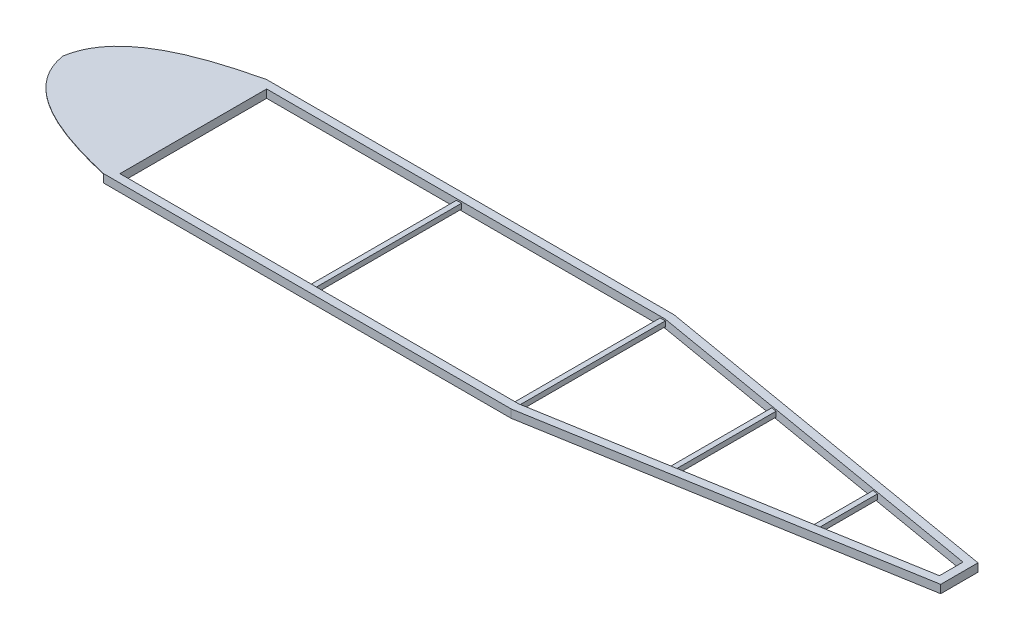
SolidWorks part; units mm, degrees
material "6061-T6 (SS)"
ref_plane "Front" through (0, 0, 0) normal (0, 0, 1) x (1, 0, 0)
ref_plane "Top" through (0, 0, 0) normal (0, 1, 0) x (1, 0, 0)
ref_plane "Right" through (0, 0, 0) normal (1, 0, 0) x (0, 0, -1)
sketch "Sketch1" plane through (0, 0, 0) normal (0, 1, 0) x (1, 0, 0)
  line L0 (0, 508) -> (0, -508)
  line L1 (0, -508) -> (2540, -508)
  line L2 (2540, -508) -> (4826, -116.205)
  line L3 (4826, -116.205) -> (4826, 116.205)
  line L4 (4826, 116.205) -> (2540, 508)
  line L5 (2540, 508) -> (0, 508)
  line L6 (2535.6782, 457.2) -> (50.8, 457.2)
  line L7 (50.8, 457.2) -> (50.8, -457.2)
  line L8 (50.8, -457.2) -> (2535.6782, -457.2)
  line L9 (2535.6782, -457.2) -> (4775.2, -73.3709)
  line L10 (4775.2, -73.3709) -> (4775.2, 73.3709)
  line L11 (4775.2, 73.3709) -> (2535.6782, 457.2)
  point P3 (0, 0)
  point P8 (4826, 0)
  dimension "D1" = 1016
  dimension "D2" = 2540
  dimension "D3" = 4826
  dimension "D4" = 232.41
  dimension "D5" = 50.8
extrude "Boss-Extrude1" add sketch "Sketch1" along normal blind 50.8
ref_plane "Plane1" through (0, 3.175, 0) normal (0, 1, 0) x (1, 0, 0)
sketch "Sketch2" plane through (0, 3.175, 0) normal (0, 1, 0) x (1, 0, 0)
  line L6 (2535.9483, 460.375) -> (47.625, 460.375)
  line L7 (47.625, 460.375) -> (47.625, -460.375)
  line L8 (47.625, -460.375) -> (2535.9483, -460.375)
  line L9 (2535.9483, -460.375) -> (4778.375, -76.048)
  line L10 (4778.375, -76.048) -> (4778.375, 76.048)
  line L11 (4778.375, 76.048) -> (2535.9483, 460.375)
  line L12 (3.175, -504.825) -> (2539.7299, -504.825)
  line L13 (2539.7299, -504.825) -> (4822.825, -113.5279)
  line L14 (4822.825, -113.5279) -> (4822.825, 113.5279)
  line L15 (4822.825, 113.5279) -> (2539.7299, 504.825)
  line L16 (2539.7299, 504.825) -> (3.175, 504.825)
  line L17 (3.175, 504.825) -> (3.175, -504.825)
  line L18 (3.175, -504.825) -> (2539.7299, -504.825)
  line L19 (2539.7299, -504.825) -> (4822.825, -113.5279)
  line L20 (4822.825, -113.5279) -> (4822.825, 113.5279)
  line L21 (4822.825, 113.5279) -> (2539.7299, 504.825)
  line L22 (2539.7299, 504.825) -> (3.175, 504.825)
  line L23 (3.175, 504.825) -> (3.175, -504.825)
  dimension "D1" = 3.175
  dimension "D2" = 44.45
extrude "Cut-Extrude1" cut sketch "Sketch2" along normal blind 44.45
sketch "Sketch3" plane through (0, 0, -457.2) normal (0, 0, 1) x (1, 0, 0)
  line L0 (2535.6782, 41.275) -> (2535.6782, 9.525)
  line L1 (2535.6782, 50.8) -> (50.8, 50.8) construction
  line L2 (1262.5032, 38.1) -> (1237.1032, 38.1)
  line L3 (2535.6782, 50.8) -> (2535.6782, 0) construction
  line L4 (2535.6782, 41.275) -> (2503.9282, 41.275)
  line L5 (2503.9282, 41.275) -> (2503.9282, 9.525)
  line L6 (2503.9282, 9.525) -> (2535.6782, 9.525)
  line L7 (2532.5032, 38.1) -> (2507.1032, 38.1)
  line L8 (2507.1032, 38.1) -> (2507.1032, 12.7)
  line L9 (2507.1032, 12.7) -> (2532.5032, 12.7)
  line L10 (2532.5032, 38.1) -> (2532.5032, 12.7)
  line L11 (1265.6782, 41.275) -> (1233.9282, 41.275)
  line L12 (1233.9282, 41.275) -> (1233.9282, 9.525)
  line L13 (1233.9282, 9.525) -> (1265.6782, 9.525)
  line L14 (1237.1032, 12.7) -> (1262.5032, 12.7)
  line L15 (1265.6782, 41.275) -> (1265.6782, 9.525)
  line L16 (1262.5032, 38.1) -> (1262.5032, 12.7)
  line L17 (1237.1032, 38.1) -> (1237.1032, 12.7)
  point P5 (2535.6782, 25.4)
  point P8 (2535.6782, 25.4)
  dimension "D1" = 9.525
  dimension "D2" = 3.175
  dimension "D3" = 2
extrude "Boss-Extrude2" add sketch "Sketch3" along normal up to next
sketch "Sketch4" plane through (50.8, 0, 0) normal (1, 0, 0) x (0, 0, -1)
  line L0 (0, 50.8) -> (0, 0) construction
  line L1 (457.2, 50.8) -> (-457.2, 50.8) construction
  point P7 (0, 25.4)
sketch "Sketch5" plane through (4775.2, 0, 0) normal (-1, 0, 0) x (0, 0, 1)
  line L0 (0, 50.8) -> (0, 0) construction
  line L1 (73.3709, 50.8) -> (-73.3709, 50.8) construction
  line L2 (73.3709, 0) -> (-73.3709, 0) construction
  point P6 (0, 25.4)
ref_plane "Plane2" through (0, 0, 0) normal (0, 0, 1) x (1, 0, 0)
sketch "Sketch8" plane through (0, 0, 0) normal (0, 0, 1) x (1, 0, 0)
  line L0 (50.8, 25.4) -> (4775.2, 25.4) construction
  line L1 (50.8, 50.8) -> (50.8, 0) construction
  line L2 (3340.1, 38.1) -> (3365.5, 38.1)
  line L3 (3336.925, 41.275) -> (3368.675, 41.275)
  line L4 (3336.925, 41.275) -> (3336.925, 9.525)
  line L5 (3336.925, 9.525) -> (3368.675, 9.525)
  line L6 (3368.675, 41.275) -> (3368.675, 9.525)
  line L7 (3336.925, 41.275) -> (3368.675, 9.525) construction
  line L8 (3336.925, 9.525) -> (3368.675, 41.275) construction
  line L9 (3365.5, 38.1) -> (3365.5, 12.7)
  line L10 (3340.1, 12.7) -> (3365.5, 12.7)
  line L11 (3340.1, 38.1) -> (3340.1, 12.7)
  line L12 (4102.1, 38.1) -> (4127.5, 38.1)
  line L13 (4098.925, 41.275) -> (4130.675, 41.275)
  line L14 (4098.925, 41.275) -> (4098.925, 9.525)
  line L15 (4098.925, 9.525) -> (4130.675, 9.525)
  line L16 (4130.675, 41.275) -> (4130.675, 9.525)
  line L17 (4098.925, 41.275) -> (4130.675, 9.525) construction
  line L18 (4098.925, 9.525) -> (4130.675, 41.275) construction
  line L19 (4127.5, 38.1) -> (4127.5, 12.7)
  line L20 (4102.1, 12.7) -> (4127.5, 12.7)
  line L21 (4102.1, 38.1) -> (4102.1, 12.7)
  point P5 (4114.8, 25.4)
  point P6 (3352.8, 25.4)
  point P7 (3352.8, 25.4)
  point P16 (4114.8, 25.4)
  dimension "D1" = 3302
  dimension "D2" = 4064
  dimension "D3" = 31.75
  dimension "D5" = 31.75
  dimension "D4" = 3.175
  dimension "D6" = 3.175
extrude "Boss-Extrude3" add sketch "Sketch8" along normal up to next and the other way up to next separate body
sketch "Sketch9" plane through (0, 0, 0) normal (0, -1, 0) x (-1, 0, 0)
  line L0 (0, 0) -> (762, 0) construction
  spline S0 degree 3 poles (762, 0) (716.4964, 292.4781) (357.6366, 425.2706) (0, 508) knots 0 0 0 0 1 1 1 1 construction
  spline S1 degree 3 poles (762, 0) (761.894, 7.5883) (761.4727, 15.179) (760.7298, 22.7316) (760.0533, 29.61) (759.1092, 36.4674) (757.9006, 43.2726) (756.6901, 50.0881) (755.2125, 56.8614) (753.4779, 63.5627) (751.7288, 70.3195) (749.7158, 77.0132) (747.4555, 83.6167) (745.1701, 90.2934) (742.6288, 96.8874) (739.8534, 103.3758) (738.1962, 107.25) (736.4547, 111.0892) (734.6339, 114.8893) (731.4584, 121.517) (728.0387, 128.0323) (724.4035, 134.4194) (720.7275, 140.8784) (716.827, 147.214) (712.7317, 153.4157) (708.5736, 159.7126) (704.2106, 165.878) (699.672, 171.9064) (695.0489, 178.047) (690.2397, 184.051) (685.2725, 189.9168) (680.8902, 195.0919) (676.3822, 200.1628) (671.7659, 205.1303) (665.6534, 211.7079) (659.3465, 218.1089) (652.8803, 224.3391) (646.3076, 230.6717) (639.5656, 236.8322) (632.6848, 242.8287) (625.6762, 248.9366) (618.5197, 254.8778) (611.2418, 260.6622) (603.818, 266.5626) (596.2645, 272.3026) (588.6046, 277.8929) (580.7835, 283.6008) (572.8483, 289.155) (564.8193, 294.5665) (556.6165, 300.0953) (548.3131, 305.4771) (539.9266, 310.7232) (531.3558, 316.0847) (522.6959, 321.3061) (513.9625, 326.3986) (505.0357, 331.6038) (496.0301, 336.6757) (486.9592, 341.6254) (477.6875, 346.6846) (468.3459, 351.6172) (458.9463, 356.4345) (449.8647, 361.0887) (440.7278, 365.6365) (431.5398, 370.0769) (417.6994, 376.7657) (403.7394, 383.2124) (389.6759, 389.4185) (375.5433, 395.6552) (361.302, 401.6507) (346.9696, 407.4133) (332.5275, 413.22) (317.989, 418.7917) (303.3721, 424.1433) (288.6042, 429.5501) (273.753, 434.7336) (258.8362, 439.715) (248.4017, 443.1996) (237.934, 446.5858) (227.4387, 449.8826) (209.7129, 455.4507) (191.9058, 460.7641) (174.0418, 465.8712) (155.576, 471.1504) (137.0485, 476.2173) (118.4733, 481.098) (99.349, 486.1229) (80.1708, 490.9464) (60.9475, 495.5782) (41.2639, 500.321) (21.5311, 504.8633) (1.7573, 509.2143) (-18.4148, 513.6529) (-38.6316, 517.8929) (-58.8854, 521.9424) (-79.4953, 526.0631) (-100.1455, 529.987) (-120.8289, 533.7214) (-141.8387, 537.5147) (-162.8847, 541.1122) (-183.96, 544.5225) (-205.3429, 547.9825) (-226.7575, 551.2508) (-248.1972, 554.3395) (-269.9348, 557.471) (-291.6997, 560.4182) (-313.4856, 563.1942) (-335.5661, 566.0078) (-357.6696, 568.6457) (-379.7905, 571.1224) (-402.2065, 573.6321) (-424.6415, 575.9765) (-447.0906, 578.1706) (-469.1828, 580.33) (-491.2896, 582.3449) (-513.4076, 584.2224) (-544.1627, 586.833) (-574.9413, 589.1776) (-605.7358, 591.2728) (-636.8644, 593.3907) (-668.0114, 595.2538) (-699.1696, 596.8789) (-730.6761, 598.5222) (-762.1961, 599.9224) (-793.7236, 601.0959) (-825.6105, 602.2827) (-857.5069, 603.2374) (-889.4073, 603.9756) (-921.6764, 604.7223) (-953.9512, 605.2474) (-986.2272, 605.567) (-1018.8824, 605.8905) (-1051.5401, 606.0037) (-1084.1967, 605.9229) (-1117.2416, 605.8412) (-1150.2865, 605.5602) (-1183.3281, 605.092) (-1220.009, 604.5723) (-1256.6873, 603.8217) (-1293.3592, 602.8567) (-1334.0306, 601.7863) (-1374.6957, 600.4525) (-1415.3506, 598.8756) (-1456.5369, 597.2781) (-1497.7141, 595.4304) (-1538.8789, 593.3506) (-1580.5702, 591.2442) (-1622.2501, 588.8995) (-1663.9157, 586.3353) (-1706.1142, 583.7383) (-1748.2992, 580.9163) (-1790.4687, 577.8849) (-1833.1726, 574.8151) (-1875.8616, 571.5303) (-1918.5338, 568.0466) (-1929.8264, 567.1247) (-1941.1178, 566.1888) (-1952.4081, 565.2393) (-2002.9099, 560.9922) (-2053.3894, 556.4729) (-2103.8444, 551.7014) (-2154.9421, 546.8692) (-2206.0159, 541.778) (-2257.0641, 536.448) (-2308.7647, 531.0499) (-2360.4403, 525.4071) (-2412.0896, 519.5375) (-2464.3943, 513.5933) (-2516.6731, 507.4163) (-2568.925, 501.0244) (-2621.8363, 494.5519) (-2674.7212, 487.8596) (-2727.5786, 480.9607) (-2781.0866, 473.9769) (-2834.5673, 466.7813) (-2888.0201, 459.387) (-2942.1116, 451.9044) (-2996.1754, 444.2184) (-3050.2108, 436.3403) (-3104.8721, 428.3709) (-3159.5051, 420.2048) (-3214.1094, 411.8534) (-3269.3265, 403.4083) (-3324.515, 394.7733) (-3379.6738, 385.9552) (-3389.7474, 384.3448) (-3399.82, 382.7283) (-3409.8917, 381.1057) (-3476.9763, 370.298) (-3544.0183, 359.2218) (-3611.0158, 347.8864) (-3678.3464, 336.4947) (-3745.6331, 324.8402) (-3812.8739, 312.9296) (-3880.4002, 300.9684) (-3947.8812, 288.7487) (-4015.3148, 276.2757) (-4082.9992, 263.7563) (-4150.6374, 250.9849) (-4218.2249, 237.9529) (-4285.8748, 224.9089) (-4353.4743, 211.6002) (-4421.0157, 198.0052) (-4488.5919, 184.4031) (-4556.111, 170.5146) (-4623.5816, 156.398) (-4691.2032, 142.2498) (-4758.7861, 127.9133) (-4826.3049, 113.2824) (-4845.4402, 109.1358) (-4864.5698, 104.9624) (-4883.692, 100.7559) (-4931.9643, 90.137) (-4980.1912, 79.3076) (-5028.3462, 68.1689) (-5080.5978, 56.0827) (-5132.7641, 43.6303) (-5184.943, 31.2337) (-5221.7426, 22.4909) (-5258.5546, 13.7995) (-5295.3891, 5.2046) (-5304.5979, 3.0559) (-5313.8133, 0.9345) (-5323.0051, -1.2857) (-5325.4662, -1.8802) (-5327.9292, -2.4708) (-5330.3696, -3.1451) (-5330.9805, -3.3139) (-5331.5939, -3.479) (-5332.1896, -3.6953) (-5332.3395, -3.7497) (-5332.4912, -3.8048) (-5332.6281, -3.8867) (-5332.6575, -3.9043) (-5332.687, -3.9235) (-5332.7102, -3.9486) (-5332.7178, -3.9569) (-5332.7248, -3.9661) (-5332.7296, -3.9762) (-5332.7326, -3.9825) (-5332.7348, -3.9894) (-5332.7357, -3.9963) (-5332.7367, -4.0032) (-5332.7364, -4.0104) (-5332.735, -4.0173) (-5332.7328, -4.0279) (-5332.728, -4.038) (-5332.722, -4.047) (-5332.7161, -4.0558) (-5332.709, -4.0639) (-5332.7013, -4.0714) (-5332.683, -4.0894) (-5332.6618, -4.1043) (-5332.6401, -4.118) (-5332.5737, -4.1598) (-5332.5014, -4.1919) (-5332.4292, -4.2225) (-5332.1406, -4.3447) (-5331.84, -4.4374) (-5331.5404, -4.5295) (-5330.7484, -4.7728) (-5329.9474, -4.986) (-5329.146, -5.1964) (-5327.5432, -5.6171) (-5325.9341, -6.0133) (-5324.324, -6.4051) (-5321.1041, -7.1886) (-5317.8786, -7.9485) (-5314.6526, -8.7063) (-5308.2007, -10.2218) (-5301.7452, -11.722) (-5295.2906, -13.2257) (-5282.3811, -16.233) (-5269.4733, -19.247) (-5256.5689, -22.2759) (-5230.7602, -28.3339) (-5204.9641, -34.4458) (-5179.1708, -40.569) (-5127.5844, -52.8153) (-5076.0067, -65.102) (-5024.3434, -77.0199) (-4971.9573, -89.1046) (-4919.4869, -100.8259) (-4866.9664, -112.3124) (-4815.9178, -123.477) (-4764.8209, -134.4207) (-4713.7019, -145.2587) (-4641.8702, -160.4881) (-4569.9899, -175.4913) (-4498.0506, -190.2039) (-4429.9844, -204.1243) (-4361.8627, -217.7766) (-4293.6872, -231.1517) (-4225.9656, -244.4377) (-4158.1909, -257.4559) (-4090.3662, -270.2057) (-4023.3924, -282.7955) (-3956.3688, -295.1231) (-3889.2996, -307.1941) (-3821.2854, -319.4352) (-3753.2237, -331.4145) (-3685.1179, -343.1349) (-3616.8136, -354.8895) (-3548.464, -366.3833) (-3480.0717, -377.614) (-3412.2274, -388.7548) (-3344.3397, -399.6344) (-3276.4073, -410.2242) (-3209.9656, -420.5816) (-3143.4797, -430.6598) (-3076.9509, -440.4423) (-3011.6266, -450.0477) (-2946.26, -459.3698) (-2880.8532, -468.3963) (-2816.7441, -477.2436) (-2752.595, -485.8059) (-2688.4066, -494.0575) (-2625.6443, -502.1258) (-2562.8432, -509.8984) (-2500.0045, -517.3488) (-2438.7163, -524.6154) (-2377.3907, -531.5747) (-2316.0295, -538.1971) (-2262.6286, -543.9604) (-2209.1995, -549.4691) (-2155.7439, -554.7007) (-2104.2941, -559.7361) (-2052.8185, -564.5149) (-2001.3193, -569.0172) (-1951.8403, -573.343) (-1902.3383, -577.4143) (-1852.8156, -581.2072) (-1805.3018, -584.8463) (-1757.7675, -588.2291) (-1710.2158, -591.334) (-1664.5644, -594.3149) (-1618.8954, -597.0405) (-1573.2123, -599.487) (-1529.3985, -601.8334) (-1485.57, -603.923) (-1441.7308, -605.734) (-1415.6122, -606.8129) (-1389.4892, -607.793) (-1363.363, -608.6696) (-1322.036, -610.0561) (-1280.6994, -611.1836) (-1239.3578, -612.0287) (-1199.1306, -612.851) (-1158.8969, -613.406) (-1118.6622, -613.6717) (-1079.4966, -613.9304) (-1040.328, -613.916) (-1001.1628, -613.603) (-963.1123, -613.2989) (-925.0629, -612.7121) (-887.0217, -611.8166) (-850.0197, -610.9456) (-813.0232, -609.7826) (-776.0404, -608.3046) (-767.1368, -607.9488) (-758.234, -607.5747) (-749.3319, -607.1821) (-716.0454, -605.7139) (-682.7693, -603.9865) (-649.5108, -601.9821) (-617.038, -600.025) (-584.5798, -597.8037) (-552.1447, -595.2986) (-520.5153, -592.8557) (-488.9054, -590.1426) (-457.3243, -587.138) (-426.8197, -584.2358) (-396.3393, -581.0608) (-365.8965, -577.569) (-336.6327, -574.2124) (-307.4007, -570.5626) (-278.2149, -566.5847) (-250.0621, -562.7477) (-221.949, -558.6048) (-193.8905, -554.1303) (-166.6643, -549.7885) (-139.4862, -545.1324) (-112.3702, -540.1484) (-99.1738, -537.7228) (-85.9914, -535.2198) (-72.8247, -532.6381) (-48.977, -527.9621) (-25.1784, -523.0277) (-1.4403, -517.8234) (21.8177, -512.7243) (45.0206, -507.3655) (68.1549, -501.7313) (90.7417, -496.2303) (113.2662, -490.466) (135.7128, -484.4187) (157.2513, -478.6161) (178.7246, -472.5616) (200.0975, -466.1763) (217.7682, -460.897) (235.3725, -455.388) (252.8848, -449.6049) (269.1499, -444.2336) (285.339, -438.6247) (301.4293, -432.7503) (316.7379, -427.1613) (331.9608, -421.3306) (347.0776, -415.2418) (361.7148, -409.3462) (376.2565, -403.207) (390.6846, -396.8166) (404.8478, -390.5434) (418.9056, -384.0263) (432.8421, -377.2645) (446.5368, -370.6199) (460.1206, -363.7409) (473.5727, -356.618) (486.3898, -349.8314) (499.0895, -342.8166) (511.6365, -335.5427) (523.2094, -328.8335) (534.6568, -321.9013) (545.9424, -314.7194) (556.6742, -307.8899) (567.2646, -300.8314) (577.6733, -293.519) (587.5912, -286.5513) (597.3497, -279.3491) (606.9033, -271.8897) (616.0305, -264.7632) (624.9771, -257.397) (633.6922, -249.7719) (641.0778, -243.3098) (648.3022, -236.6573) (655.3266, -229.8043) (660.6341, -224.6262) (665.8303, -219.3309) (670.8951, -213.9152) (676.979, -207.41) (682.8784, -200.7258) (688.5535, -193.8611) (694.0231, -187.2449) (699.2897, -180.4542) (704.3126, -173.4928) (709.1811, -166.7455) (713.826, -159.8299) (718.2067, -152.7562) (722.4824, -145.852) (726.5119, -138.7879) (730.2559, -131.5815) (732.7036, -126.8702) (735.0312, -122.0944) (737.2281, -117.2612) (740.2111, -110.6984) (742.9562, -104.0217) (745.4389, -97.2539) (747.8881, -90.5776) (750.0853, -83.8029) (752.0113, -76.9573) (753.9282, -70.1439) (755.5794, -63.2499) (756.9522, -56.3063) (758.1709, -50.142) (759.1719, -43.9305) (759.9514, -37.6954) (760.8114, -30.8168) (761.4028, -23.8996) (761.7275, -16.9751) (761.8818, -13.6856) (761.9761, -10.3926) (762.0112, -7.0997) (762.02, -6.2765) (762.0251, -5.4534) (762.0267, -4.6302) (762.0271, -4.4244) (762.0274, -4.2186) (762.0274, -4.0128) (762.0274, -3.9099) (762.0273, -3.807) (762.0272, -3.7041) (762.0268, -3.2926) (762.0256, -2.881) (762.0235, -2.4694) (762.0193, -1.6462) (762.0115, -0.8231) (762, 0) (761.894, 7.5883) (761.4727, 15.179) knots -0.00247 0 0 0 0.023093 0.023093 0.023093 0.044323 0.044323 0.044323 0.065644 0.065644 0.065644 0.087071 0.087071 0.087071 0.108542 0.108542 0.108542 0.121321 0.121321 0.121321 0.143745 0.143745 0.143745 0.166493 0.166493 0.166493 0.189561 0.189561 0.189561 0.212943 0.212943 0.212943 0.233608 0.233608 0.233608 0.261232 0.261232 0.261232 0.289509 0.289509 0.289509 0.318426 0.318426 0.318426 0.347971 0.347971 0.347971 0.378134 0.378134 0.378134 0.408905 0.408905 0.408905 0.440277 0.440277 0.440277 0.472241 0.472241 0.472241 0.504793 0.504793 0.504793 0.536209 0.536209 0.536209 0.583605 0.583605 0.583605 0.631268 0.631268 0.631268 0.679278 0.679278 0.679278 0.727722 0.727722 0.727722 0.761616 0.761616 0.761616 0.819 0.819 0.819 0.878436 0.878436 0.878436 0.93971 0.93971 0.93971 1.002506 1.002506 1.002506 1.066595 1.066595 1.066595 1.131816 1.131816 1.131816 1.198048 1.198048 1.198048 1.265206 1.265206 1.265206 1.33324 1.33324 1.33324 1.402121 1.402121 1.402121 1.471838 1.471838 1.471838 1.540427 1.540427 1.540427 1.635867 1.635867 1.635867 1.732392 1.732392 1.732392 1.83002 1.83002 1.83002 1.928761 1.928761 1.928761 2.028626 2.028626 2.028626 2.129629 2.129629 2.129629 2.231784 2.231784 2.231784 2.345183 2.345183 2.345183 2.470987 2.470987 2.470987 2.598453 2.598453 2.598453 2.727549 2.727549 2.727549 2.858281 2.858281 2.858281 2.990641 2.990641 2.990641 3.025666 3.025666 3.025666 3.182369 3.182369 3.182369 3.341116 3.341116 3.341116 3.501923 3.501923 3.501923 3.664786 3.664786 3.664786 3.829708 3.829708 3.829708 3.996651 3.996651 3.996651 4.165573 4.165573 4.165573 4.336427 4.336427 4.336427 4.509165 4.509165 4.509165 4.540709 4.540709 4.540709 4.750839 4.750839 4.750839 4.962045 4.962045 4.962045 5.174166 5.174166 5.174166 5.387081 5.387081 5.387081 5.600185 5.600185 5.600185 5.813379 5.813379 5.813379 6.02702 6.02702 6.02702 6.087562 6.087562 6.087562 6.240403 6.240403 6.240403 6.406243 6.406243 6.406243 6.523202 6.523202 6.523202 6.552443 6.552443 6.552443 6.560272 6.560272 6.560272 6.562232 6.562232 6.562232 6.562725 6.562725 6.562725 6.562831 6.562831 6.562831 6.562865 6.562865 6.562865 6.562887 6.562887 6.562887 6.562908 6.562908 6.562908 6.562942 6.562942 6.562942 6.562974 6.562974 6.562974 6.563053 6.563053 6.563053 6.563294 6.563294 6.563294 6.564257 6.564257 6.564257 6.566803 6.566803 6.566803 6.571895 6.571895 6.571895 6.582078 6.582078 6.582078 6.602444 6.602444 6.602444 6.643175 6.643175 6.643175 6.724636 6.724636 6.724636 6.88756 6.88756 6.88756 7.052769 7.052769 7.052769 7.213347 7.213347 7.213347 7.438994 7.438994 7.438994 7.652498 7.652498 7.652498 7.864574 7.864574 7.864574 8.074029 8.074029 8.074029 8.286519 8.286519 8.286519 8.499701 8.499701 8.499701 8.711236 8.711236 8.711236 8.918178 8.918178 8.918178 9.121409 9.121409 9.121409 9.320627 9.320627 9.320627 9.515423 9.515423 9.515423 9.705397 9.705397 9.705397 9.870695 9.870695 9.870695 10.029744 10.029744 10.029744 10.182492 10.182492 10.182492 10.328964 10.328964 10.328964 10.469484 10.469484 10.469484 10.604137 10.604137 10.604137 10.684331 10.684331 10.684331 10.811221 10.811221 10.811221 10.934718 10.934718 10.934718 11.054938 11.054938 11.054938 11.171715 11.171715 11.171715 11.285253 11.285253 11.285253 11.312581 11.312581 11.312581 11.414825 11.414825 11.414825 11.514723 11.514723 11.514723 11.612181 11.612181 11.612181 11.706331 11.706331 11.706331 11.796812 11.796812 11.796812 11.884026 11.884026 11.884026 11.968543 11.968543 11.968543 12.009668 12.009668 12.009668 12.084289 12.084289 12.084289 12.157547 12.157547 12.157547 12.22918 12.22918 12.22918 12.297985 12.297985 12.297985 12.354892 12.354892 12.354892 12.407722 12.407722 12.407722 12.457911 12.457911 12.457911 12.506378 12.506378 12.506378 12.553768 12.553768 12.553768 12.600094 12.600094 12.600094 12.644189 12.644189 12.644189 12.684996 12.684996 12.684996 12.723871 12.723871 12.723871 12.760907 12.760907 12.760907 12.796187 12.796187 12.796187 12.825907 12.825907 12.825907 12.848338 12.848338 12.848338 12.875421 12.875421 12.875421 12.901587 12.901587 12.901587 12.926902 12.926902 12.926902 12.951434 12.951434 12.951434 12.96743 12.96743 12.96743 12.989261 12.989261 12.989261 13.010814 13.010814 13.010814 13.032154 13.032154 13.032154 13.051042 13.051042 13.051042 13.071882 13.071882 13.071882 13.081763 13.081763 13.081763 13.084232 13.084232 13.084232 13.08485 13.08485 13.08485 13.085159 13.085159 13.085159 13.086393 13.086393 13.086393 13.088863 13.088863 13.088863 13.111956 13.111956 13.111956 only from (762, 0) to (762, 0) construction
  spline S2 degree 3 poles (762, 0) (716.4964, -292.4781) (357.6366, -425.2706) (0, -508) knots 0 0 0 0 1 1 1 1 construction
  dimension "D1" = 762
ref_plane "Plane3" through (0, 50.8, 0) normal (0, 1, 0) x (1, 0, 0)
sketch "Sketch11" plane through (0, 50.8, 0) normal (0, 1, 0) x (1, 0, 0)
  line L0 (0, 0) -> (-762, 0) construction
  line L1 (0, 0) -> (-762, 0) construction
  line L2 (0, 508) -> (0, -508)
  spline S0 degree 3 poles (1262.4304, -2137.367) (-4867.5971, 2107.826) (5635.2482, -616.0416) (-2454.1802, 1966.0356) knots -1.279799 -1.279799 -1.279799 -1.279799 3.540131 3.540131 3.540131 3.540131 only from (-762, 0) to (0, 508) construction
  spline S1 degree 3 poles (1262.4304, 2137.367) (-4867.5971, -2107.826) (5635.2482, 616.0416) (-2454.1802, -1966.0356) knots -1.279799 -1.279799 -1.279799 -1.279799 3.540131 3.540131 3.540131 3.540131 only from (-762, 0) to (0, -508) construction
  spline S2 degree 3 poles (-762, 0) (-716.4964, 292.4781) (-357.6366, 425.2706) (0, 508) knots 0 0 0 0 1 1 1 1
  spline S3 degree 3 poles (-762, 0) (-716.4964, -292.4781) (-357.6366, -425.2706) (0, -508) knots 0 0 0 0 1 1 1 1
extrude "Boss-Extrude5" add sketch "Sketch11" against normal blind 3.175
